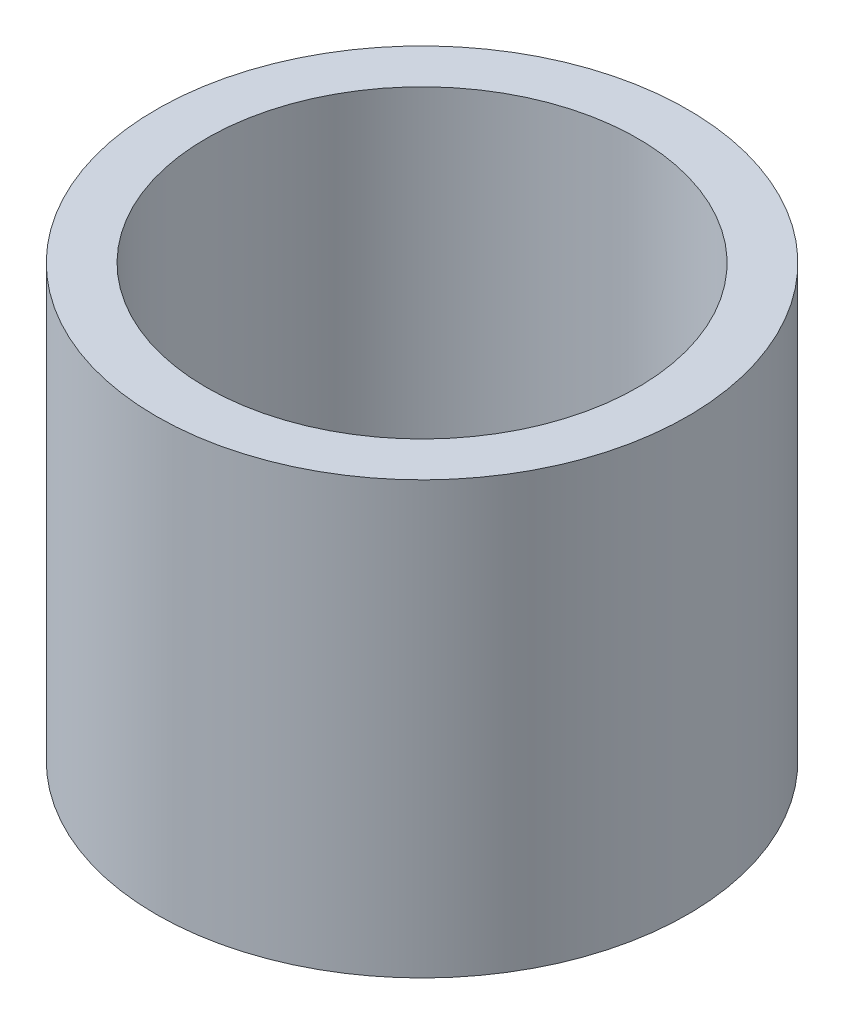
SolidWorks part; units mm, degrees
material "1.4000 (X6Cr13)"
ref_plane "Plan de face" through (0, 0, 0) normal (0, 0, 1) x (1, 0, 0)
ref_plane "Plan de dessus" through (0, 0, 0) normal (0, 1, 0) x (1, 0, 0)
ref_plane "Plan de droite" through (0, 0, 0) normal (1, 0, 0) x (0, 0, -1)
sketch "Esquisse1" plane through (0, 0, 0) normal (0, 0, 1) x (1, 0, 0)
  line L0 (0, 1.8358) -> (0, -2.5335) construction
  line L1 (1.54, 0) -> (1.25, 0)
  line L3 (1.25, 0) -> (1.25, 2.5)
  line L4 (1.25, 2.5) -> (1.54, 2.5)
  line L5 (1.54, 0) -> (1.54, 2.5)
  point P1 (0, 0)
  dimension "D1" = 2.5
  dimension "D2" = 3.08
  dimension "D3" = 2.5
revolve "Révolution1" add sketch "Esquisse1" angle 360 about L0
